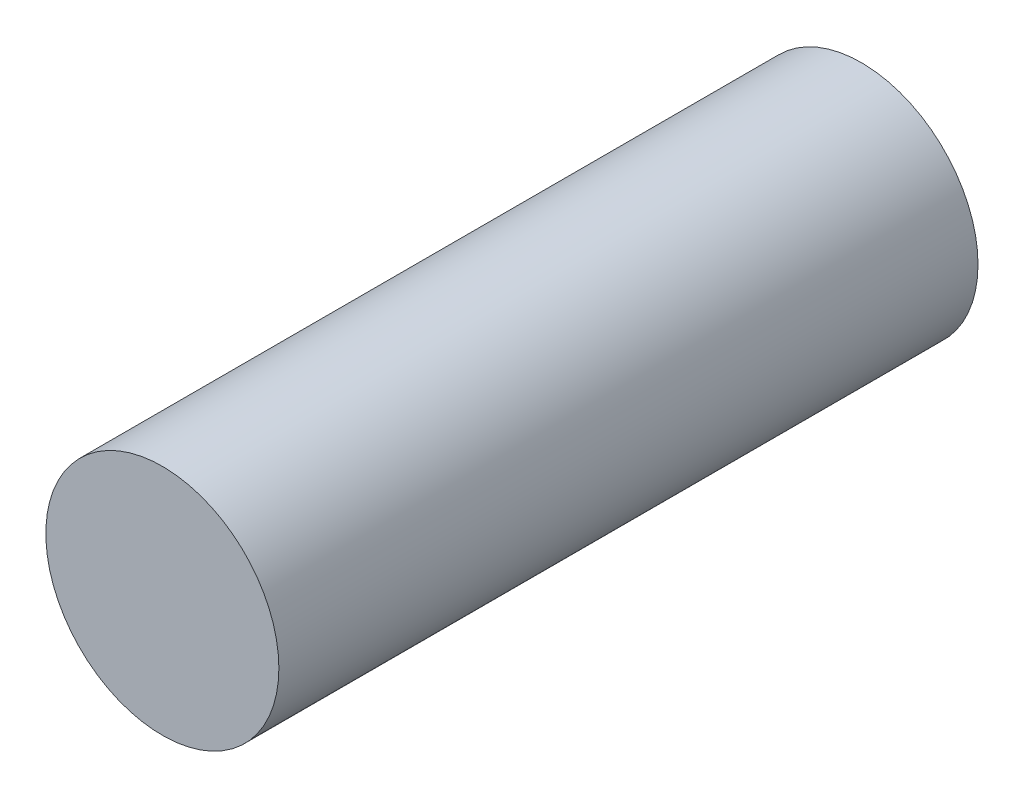
SolidWorks part; units mm, degrees
ref_plane "Front Plane" through (0, 0, 0) normal (0, 0, 1) x (1, 0, 0)
ref_plane "Top Plane" through (0, 0, 0) normal (0, 1, 0) x (1, 0, 0)
ref_plane "Right Plane" through (0, 0, 0) normal (1, 0, 0) x (0, 0, -1)
sketch "Sketch2" plane through (0, 0, 0) normal (0, 0, 1) x (1, 0, 0)
  circle A0 centre (0, 0) radius 2.5
extrude "Boss-Extrude1" add sketch "Sketch2" along normal blind 15
